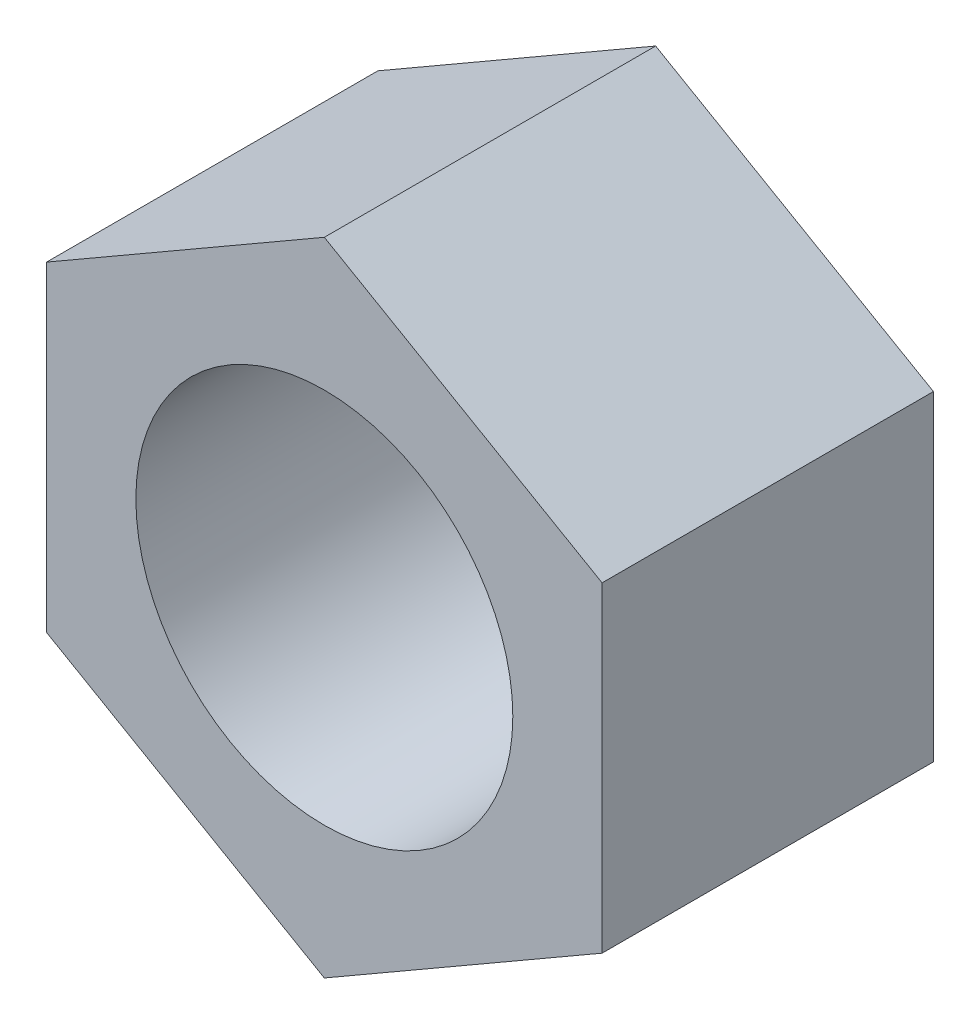
SolidWorks part; units mm, degrees
ref_plane "Front Plane" through (0, 0, 0) normal (0, 0, 1) x (1, 0, 0)
ref_plane "Top Plane" through (0, 0, 0) normal (0, 1, 0) x (1, 0, 0)
ref_plane "Right Plane" through (0, 0, 0) normal (1, 0, 0) x (0, 0, -1)
sketch "Sketch1" plane through (0, 0, 0) normal (0, 0, 1) x (1, 0, 0)
  line L1 (7, 4.0415) -> (0, 8.0829)
  line L2 (0, 8.0829) -> (-7, 4.0415)
  line L3 (-7, 4.0415) -> (-7, -4.0415)
  line L4 (-7, -4.0415) -> (0, -8.0829)
  line L5 (0, -8.0829) -> (7, -4.0415)
  line L6 (7, -4.0415) -> (7, 4.0415)
  circle A0 centre (0, 0) radius 4.75
  circle A1 centre (0, 0) radius 7 construction
  point P3 (0, 0)
  dimension "D1" = 9.5
  dimension "D2" = 14
extrude "Boss-Extrude1" add sketch "Sketch1" along normal blind 8.35
